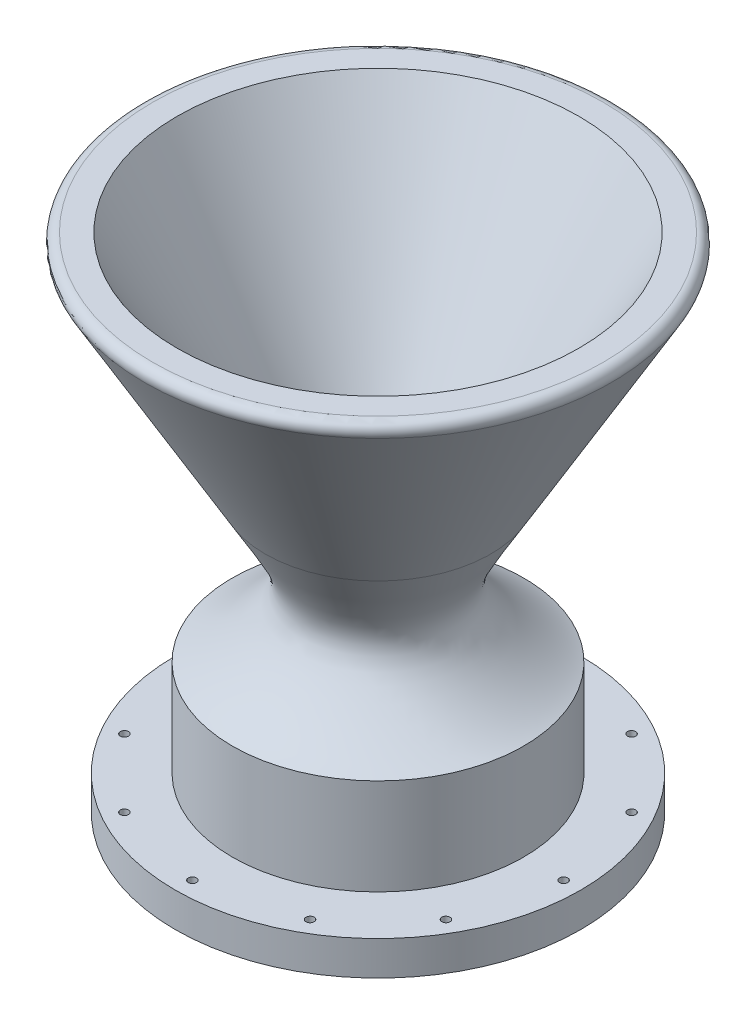
SolidWorks part; units mm, degrees
material "AISI 304"
ref_plane "Front Plane" through (0, 0, 0) normal (0, 0, 1) x (1, 0, 0)
ref_plane "Top Plane" through (0, 0, 0) normal (0, 1, 0) x (1, 0, 0)
ref_plane "Right Plane" through (0, 0, 0) normal (1, 0, 0) x (0, 0, -1)
sketch "Sketch2" plane through (0, 0, 0) normal (0, 0, 1) x (1, 0, 0)
  line L0 (0, 0) -> (56.388, 0)
  line L1 (56.388, 0) -> (56.388, 9.525)
  line L3 (6.35, 41.2962) -> (6.35, 53.9962)
  line L5 (25.493, 9.525) -> (89.279, 9.525) construction
  line L6 (-7.1602, 53.9962) -> (28.0549, 53.9962) construction
  line L7 (6.35, 53.9962) -> (55.88, 139.7846)
  line L9 (55.88, 139.7846) -> (62.656, 139.7846)
  line L10 (64.8557, 135.9746) -> (31.35, 77.9411)
  line L14 (6.35, 41.2962) -> (21.7805, 32.3874)
  line L15 (21.7805, 32.3874) -> (21.7805, 6.35)
  line L16 (21.7805, 6.35) -> (0, 6.35)
  line L17 (0, 6.35) -> (0, 0)
  line L18 (56.388, 9.525) -> (40.513, 9.525)
  line L19 (40.513, 9.525) -> (40.513, 36.2737)
  arc A0 (64.8557, 135.9746) -> (62.656, 139.7846) centre (62.656, 137.2446) ccw
  spline S0 degree 3 poles (31.35, 77.9411) (21.9947, 61.4956) (14.4962, 54.512) (35.0255, 38.6063) (40.513, 36.2737) knots 0 0 0 0 0.510149 0.739608 0.739608 0.739608 0.739608
  dimension "D4" = 2.54
  dimension "D1" = 56.388
  dimension "D2" = 9.525
  dimension "D3" = 60
  dimension "D5" = 12.7
  dimension "D6" = 6.35
  dimension "D7" = 15.875
revolve "Revolve1" add sketch "Sketch2" angle 360 about L17
sketch "Sketch5" plane through (0, 0, 0) normal (0, -1, 0) x (-1, 0, 0)
  point P0 (0, -51.6382)
  dimension "D1" = 51.6382
hole_wizard "Tap Drill for #4-40 Tap1" positions "3DSketch1" profile "Sketch6" hole size "#4-40" standard "ANSI Inch"
sketch3d "3DSketch1"
  point P0 (0, 0, 51.6382)
sketch "Sketch6" plane through (0, 0, 51.6382) normal (1, 0, 0) x (0, 0, -1)
  line L0 (0, 0) -> (0, 132.4376)
  line L1 (0, 132.4376) -> (1.1303, 132.4376)
  line L2 (1.1303, 132.4376) -> (1.1303, 0)
  line L5 (1.1303, 0) -> (0, 0)
  line L11 (0, -6.35) -> (0, 107.95) construction
  dimension "Thru Hole Dia." = 2.2606
  dimension "Thru Hole Depth" = 132.4376
pattern_circular "CirPattern2" count 12 over 360 about axis through (0, 0, 0) along (0, 1, 0) of "Tap Drill for #4-40 Tap1"
